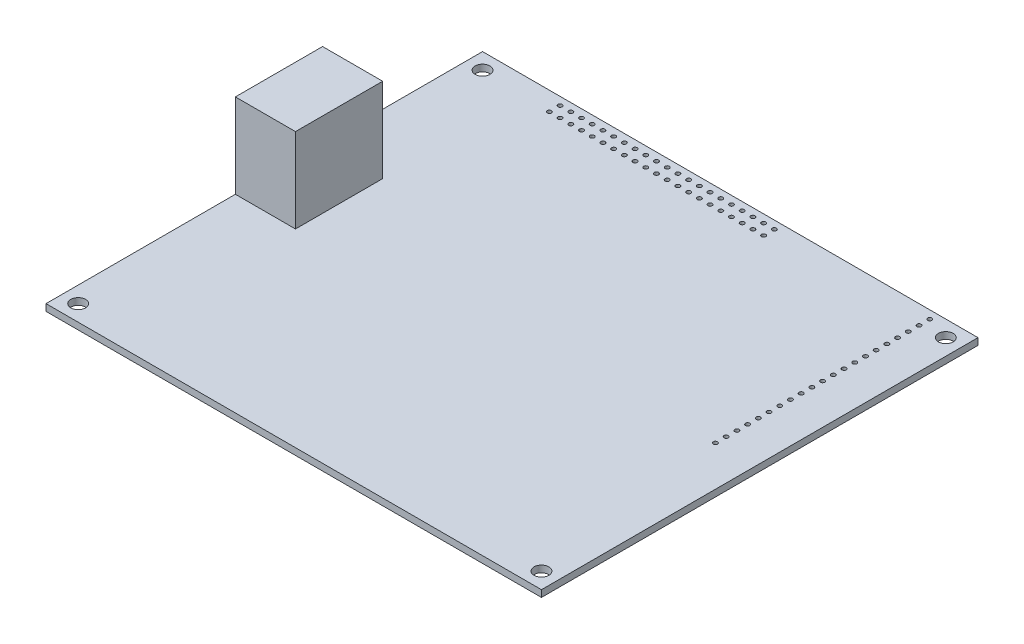
SolidWorks part; units mm, degrees
ref_plane "Front Plane" through (0, 0, 0) normal (0, 0, 1) x (1, 0, 0)
ref_plane "Top Plane" through (0, 0, 0) normal (0, 1, 0) x (1, 0, 0)
ref_plane "Right Plane" through (0, 0, 0) normal (1, 0, 0) x (0, 0, -1)
sketch "Sketch1" plane through (0, 0, 0) normal (0, 1, 0) x (1, 0, 0)
  line L0 (0, 51.7525) -> (117.475, 51.7525) construction
  line L1 (0, 0) -> (117.475, 0)
  line L2 (0, 0) -> (0, 103.505)
  line L3 (0, 103.505) -> (117.475, 103.505)
  line L4 (117.475, 0) -> (117.475, 103.505)
  circle A0 centre (3.815, 3.815) radius 1.7526
  circle A1 centre (113.66, 3.815) radius 1.7526
  circle A2 centre (113.66, 99.69) radius 1.7526
  circle A3 centre (3.815, 99.69) radius 1.7526
  dimension "D3" = 3.5052
  dimension "D1" = 117.475
  dimension "D2" = 103.505
  dimension "D4" = 3.815
  dimension "D5" = 3.815
  dimension "D6" = 3.815
extrude "Boss-Extrude1" add sketch "Sketch1" along normal blind 1.6
sketch "Sketch2" plane through (0, 1.6, 0) normal (0, 1, 0) x (1, 0, 0)
  line L0 (0, 103.505) -> (0, 0) construction
  line L1 (0, 65.577) -> (14.25, 65.577)
  line L2 (0, 65.577) -> (0, 44.901)
  line L3 (0, 44.901) -> (14.25, 44.901)
  line L4 (14.25, 65.577) -> (14.25, 44.901)
  point P6 (0, 55.239)
  dimension "D1" = 48.266
  dimension "D2" = 20.676
  dimension "D3" = 14.25
extrude "Boss-Extrude2" add sketch "Sketch2" along normal blind 20
sketch "Sketch3" plane through (0, 1.6, 0) normal (0, 1, 0) x (1, 0, 0)
  line L0 (117.475, 103.505) -> (0, 103.505) construction
  line L1 (0, 103.505) -> (0, 65.577) construction
  line L2 (20.285, 101.605) -> (22.825, 101.605) construction
  circle A0 centre (20.285, 101.605) radius 0.5
  circle A2 centre (22.825, 101.605) radius 0.5
  circle A3 centre (25.365, 101.605) radius 0.5
  circle A4 centre (27.905, 101.605) radius 0.5
  circle A5 centre (30.445, 101.605) radius 0.5
  circle A6 centre (32.985, 101.605) radius 0.5
  circle A7 centre (35.525, 101.605) radius 0.5
  circle A8 centre (38.065, 101.605) radius 0.5
  circle A9 centre (40.605, 101.605) radius 0.5
  circle A10 centre (43.145, 101.605) radius 0.5
  circle A11 centre (45.685, 101.605) radius 0.5
  circle A12 centre (48.225, 101.605) radius 0.5
  circle A13 centre (50.765, 101.605) radius 0.5
  circle A14 centre (53.305, 101.605) radius 0.5
  circle A15 centre (55.845, 101.605) radius 0.5
  circle A16 centre (58.385, 101.605) radius 0.5
  circle A17 centre (60.925, 101.605) radius 0.5
  circle A18 centre (63.465, 101.605) radius 0.5
  circle A19 centre (66.005, 101.605) radius 0.5
  circle A20 centre (68.545, 101.605) radius 0.5
  circle A21 centre (71.085, 101.605) radius 0.5
  circle A22 centre (22.825, 99.065) radius 0.5
  circle A23 centre (25.365, 99.065) radius 0.5
  circle A24 centre (27.905, 99.065) radius 0.5
  circle A25 centre (30.445, 99.065) radius 0.5
  circle A26 centre (32.985, 99.065) radius 0.5
  circle A27 centre (35.525, 99.065) radius 0.5
  circle A28 centre (38.065, 99.065) radius 0.5
  circle A29 centre (40.605, 99.065) radius 0.5
  circle A30 centre (43.145, 99.065) radius 0.5
  circle A31 centre (45.685, 99.065) radius 0.5
  circle A32 centre (48.225, 99.065) radius 0.5
  circle A33 centre (50.765, 99.065) radius 0.5
  circle A34 centre (53.305, 99.065) radius 0.5
  circle A35 centre (55.845, 99.065) radius 0.5
  circle A36 centre (58.385, 99.065) radius 0.5
  circle A37 centre (60.925, 99.065) radius 0.5
  circle A38 centre (63.465, 99.065) radius 0.5
  circle A39 centre (66.005, 99.065) radius 0.5
  circle A40 centre (68.545, 99.065) radius 0.5
  circle A41 centre (71.085, 99.065) radius 0.5
  circle A42 centre (20.285, 99.065) radius 0.5
  circle A43 centre (107.97, 101.565) radius 0.5
  circle A44 centre (113.66, 99.69) radius 1.7526 construction
  circle A45 centre (107.97, 99.025) radius 0.5
  circle A46 centre (107.97, 96.485) radius 0.5
  circle A47 centre (107.97, 93.945) radius 0.5
  circle A48 centre (107.97, 91.405) radius 0.5
  circle A49 centre (107.97, 88.865) radius 0.5
  circle A50 centre (107.97, 86.325) radius 0.5
  circle A51 centre (107.97, 83.785) radius 0.5
  circle A52 centre (107.97, 81.245) radius 0.5
  circle A53 centre (107.97, 78.705) radius 0.5
  circle A54 centre (107.97, 76.165) radius 0.5
  circle A55 centre (107.97, 73.625) radius 0.5
  circle A56 centre (107.97, 71.085) radius 0.5
  circle A57 centre (107.97, 68.545) radius 0.5
  circle A58 centre (107.97, 66.005) radius 0.5
  circle A59 centre (107.97, 63.465) radius 0.5
  circle A60 centre (107.97, 60.925) radius 0.5
  circle A61 centre (107.97, 58.385) radius 0.5
  circle A62 centre (107.97, 55.845) radius 0.5
  circle A63 centre (107.97, 53.305) radius 0.5
  circle A64 centre (107.97, 50.765) radius 0.5
  dimension "D1" = 1
  dimension "D8" = 1.94
  dimension "D9" = 1
  dimension "D2" = 1.9
  dimension "D3" = 20.285
  dimension "D6" = 2.54
  dimension "D7" = 2.54
  dimension "D10" = 5.69
  dimension "D12" = 2.54
  dimension "D4" = 21
  dimension "D5" = 2
  dimension "D11" = 21
extrude "Cut-Extrude1" cut sketch "Sketch3" against normal through all
